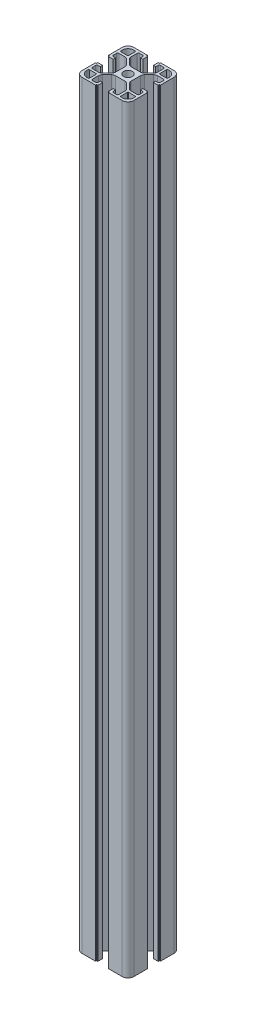
SolidWorks part; units mm, degrees
ref_plane "Front Plane" through (0, 0, 0) normal (0, 0, 1) x (1, 0, 0)
ref_plane "Top Plane" through (0, 0, 0) normal (0, 1, 0) x (1, 0, 0)
ref_plane "Right Plane" through (0, 0, 0) normal (1, 0, 0) x (0, 0, -1)
sketch "Sketch1" plane through (0, 0, 0) normal (0, 1, 0) x (1, 0, 0)
  line L0 (84.1702, 31.7204) -> (84.1702, 42.1204)
  line L1 (44.1702, 62.7204) -> (44.1702, 52.3204)
  line L2 (48.6702, 27.2204) -> (59.0702, 27.2204)
  line L3 (79.6702, 67.2204) -> (69.2702, 67.2204)
  line L4 (84.1702, 52.3204) -> (84.1702, 62.7204)
  line L6 (44.1702, 42.1204) -> (44.1702, 31.7204)
  line L7 (69.2702, 27.2204) -> (79.6702, 27.2204)
  line L10 (44.1702, 42.1204) -> (44.7702, 42.1204)
  line L11 (44.9702, 42.3204) -> (44.9702, 42.9204)
  line L12 (48.6702, 43.1204) -> (45.1702, 43.1204)
  line L13 (48.6702, 41.3204) -> (48.6702, 43.1204)
  line L14 (46.9702, 41.3204) -> (48.6702, 41.3204)
  line L15 (45.9702, 37.9704) -> (45.9702, 40.3204)
  line L16 (51.6169, 36.9704) -> (46.9702, 36.9704)
  line L17 (57.2915, 41.4024) -> (53.7382, 37.8491)
  line L18 (58.1702, 50.9171) -> (58.1702, 43.5237)
  line L19 (53.7382, 56.5917) -> (57.2915, 53.0384)
  line L20 (46.9702, 57.4704) -> (51.6169, 57.4704)
  line L21 (45.9702, 54.1204) -> (45.9702, 56.4704)
  line L22 (48.6702, 53.1204) -> (46.9702, 53.1204)
  line L23 (48.6702, 51.3204) -> (48.6702, 53.1204)
  line L24 (45.1702, 51.3204) -> (48.6702, 51.3204)
  line L25 (44.9702, 51.5204) -> (44.9702, 52.1204)
  line L26 (44.7702, 52.3204) -> (44.1702, 52.3204)
  line L28 (59.0702, 67.2204) -> (48.6702, 67.2204)
  line L29 (59.0702, 67.2204) -> (59.0702, 66.6204)
  line L30 (59.2702, 66.4204) -> (60.0702, 66.4204)
  line L31 (60.0702, 62.7204) -> (60.0702, 66.4204)
  line L32 (58.2702, 62.7204) -> (60.0702, 62.7204)
  line L33 (58.2702, 64.4204) -> (58.2702, 62.7204)
  line L34 (54.9202, 65.4204) -> (57.2702, 65.4204)
  line L35 (53.9202, 59.7737) -> (53.9202, 64.4204)
  line L36 (58.3522, 54.0991) -> (54.7989, 57.6524)
  line L37 (67.8669, 53.2204) -> (60.4735, 53.2204)
  line L38 (73.5415, 57.6524) -> (69.9882, 54.0991)
  line L39 (74.4202, 64.4204) -> (74.4202, 59.7737)
  line L40 (71.0702, 65.4204) -> (73.4202, 65.4204)
  line L41 (70.0702, 62.7204) -> (70.0702, 64.4204)
  line L42 (68.2702, 62.7204) -> (70.0702, 62.7204)
  line L43 (68.2702, 66.2204) -> (68.2702, 62.7204)
  line L44 (68.4702, 66.4204) -> (69.2702, 66.4204)
  line L45 (69.2702, 66.4204) -> (69.2702, 67.2204)
  line L48 (84.1702, 52.3204) -> (83.5702, 52.3204)
  line L49 (83.3702, 52.1204) -> (83.3702, 51.5204)
  line L50 (79.6702, 51.3204) -> (83.1702, 51.3204)
  line L51 (79.6702, 53.1204) -> (79.6702, 51.3204)
  line L52 (81.3702, 53.1204) -> (79.6702, 53.1204)
  line L53 (82.3702, 56.4704) -> (82.3702, 54.1204)
  line L54 (76.7235, 57.4704) -> (81.3702, 57.4704)
  line L55 (71.0489, 53.0384) -> (74.6022, 56.5917)
  line L56 (70.1702, 43.5237) -> (70.1702, 50.9171)
  line L57 (74.6022, 37.8491) -> (71.0489, 41.4024)
  line L58 (81.3702, 36.9704) -> (76.7235, 36.9704)
  line L59 (82.3702, 40.3204) -> (82.3702, 37.9704)
  line L60 (79.6702, 41.3204) -> (81.3702, 41.3204)
  line L61 (79.6702, 43.1204) -> (79.6702, 41.3204)
  line L62 (83.1702, 43.1204) -> (79.6702, 43.1204)
  line L63 (83.3702, 42.9204) -> (83.3702, 42.3204)
  line L64 (83.5702, 42.1204) -> (84.1702, 42.1204)
  line L67 (69.2702, 27.2204) -> (69.2702, 27.8204)
  line L68 (69.0702, 28.0204) -> (68.4702, 28.0204)
  line L69 (68.2702, 31.7204) -> (68.2702, 28.2204)
  line L70 (70.0702, 31.7204) -> (68.2702, 31.7204)
  line L71 (70.0702, 30.0204) -> (70.0702, 31.7204)
  line L72 (73.4202, 29.0204) -> (71.0702, 29.0204)
  line L73 (74.4202, 34.6671) -> (74.4202, 30.0204)
  line L74 (69.9882, 40.3417) -> (73.5415, 36.7884)
  line L75 (60.4735, 41.2204) -> (67.8669, 41.2204)
  line L76 (54.7989, 36.7884) -> (58.3522, 40.3417)
  line L77 (53.9202, 30.0204) -> (53.9202, 34.6671)
  line L78 (57.2702, 29.0204) -> (54.9202, 29.0204)
  line L79 (58.2702, 31.7204) -> (58.2702, 30.0204)
  line L80 (60.0702, 31.7204) -> (58.2702, 31.7204)
  line L81 (60.0702, 28.2204) -> (60.0702, 31.7204)
  line L82 (59.8702, 28.0204) -> (59.2702, 28.0204)
  line L83 (59.0702, 27.8204) -> (59.0702, 27.2204)
  line L84 (82.3702, 34.6704) -> (82.3702, 33.5204)
  line L85 (76.7202, 35.1704) -> (81.8702, 35.1704)
  line L86 (76.2202, 29.5204) -> (76.2202, 34.6704)
  line L87 (77.8702, 29.0204) -> (76.7202, 29.0204)
  line L88 (51.6202, 29.0204) -> (50.4702, 29.0204)
  line L89 (52.1202, 34.6704) -> (52.1202, 29.5204)
  line L90 (46.4702, 35.1704) -> (51.6202, 35.1704)
  line L91 (45.9702, 33.5204) -> (45.9702, 34.6704)
  line L92 (45.9702, 59.7704) -> (45.9702, 60.9204)
  line L93 (51.6202, 59.2704) -> (46.4702, 59.2704)
  line L94 (52.1202, 64.9204) -> (52.1202, 59.7704)
  line L95 (50.4702, 65.4204) -> (51.6202, 65.4204)
  line L96 (76.7202, 65.4204) -> (77.8702, 65.4204)
  line L97 (76.2202, 59.7704) -> (76.2202, 64.9204)
  line L98 (81.8702, 59.2704) -> (76.7202, 59.2704)
  line L99 (82.3702, 60.9204) -> (82.3702, 59.7704)
  arc A0 (60.7702, 47.2204) -> (67.5702, 47.2204) centre (64.1702, 47.2204) ccw
  arc A1 (44.1702, 31.7204) -> (48.6702, 27.2204) centre (48.6702, 31.7204) ccw
  arc A2 (44.7702, 42.1204) -> (44.9702, 42.3204) centre (44.7702, 42.3204) ccw
  arc A3 (45.1702, 43.1204) -> (44.9702, 42.9204) centre (45.1702, 42.9204) ccw
  arc A4 (46.9702, 41.3204) -> (45.9702, 40.3204) centre (46.9702, 40.3204) ccw
  arc A5 (45.9702, 37.9704) -> (46.9702, 36.9704) centre (46.9702, 37.9704) ccw
  arc A6 (51.6169, 36.9704) -> (53.7382, 37.8491) centre (51.6169, 39.9704) ccw
  arc A7 (57.2915, 41.4024) -> (58.1702, 43.5237) centre (55.1702, 43.5237) ccw
  arc A8 (58.1702, 50.9171) -> (57.2915, 53.0384) centre (55.1702, 50.9171) ccw
  arc A9 (53.7382, 56.5917) -> (51.6169, 57.4704) centre (51.6169, 54.4704) ccw
  arc A10 (46.9702, 57.4704) -> (45.9702, 56.4704) centre (46.9702, 56.4704) ccw
  arc A11 (45.9702, 54.1204) -> (46.9702, 53.1204) centre (46.9702, 54.1204) ccw
  arc A12 (44.9702, 51.5204) -> (45.1702, 51.3204) centre (45.1702, 51.5204) ccw
  arc A13 (44.9702, 52.1204) -> (44.7702, 52.3204) centre (44.7702, 52.1204) ccw
  arc A14 (48.6702, 67.2204) -> (44.1702, 62.7204) centre (48.6702, 62.7204) ccw
  arc A15 (59.0702, 66.6204) -> (59.2702, 66.4204) centre (59.2702, 66.6204) ccw
  arc A16 (58.2702, 64.4204) -> (57.2702, 65.4204) centre (57.2702, 64.4204) ccw
  arc A17 (54.9202, 65.4204) -> (53.9202, 64.4204) centre (54.9202, 64.4204) ccw
  arc A18 (53.9202, 59.7737) -> (54.7989, 57.6524) centre (56.9202, 59.7737) ccw
  arc A19 (58.3522, 54.0991) -> (60.4735, 53.2204) centre (60.4735, 56.2204) ccw
  arc A20 (67.8669, 53.2204) -> (69.9882, 54.0991) centre (67.8669, 56.2204) ccw
  arc A21 (73.5415, 57.6524) -> (74.4202, 59.7737) centre (71.4202, 59.7737) ccw
  arc A22 (74.4202, 64.4204) -> (73.4202, 65.4204) centre (73.4202, 64.4204) ccw
  arc A23 (71.0702, 65.4204) -> (70.0702, 64.4204) centre (71.0702, 64.4204) ccw
  arc A24 (68.4702, 66.4204) -> (68.2702, 66.2204) centre (68.4702, 66.2204) ccw
  arc A25 (84.1702, 62.7204) -> (79.6702, 67.2204) centre (79.6702, 62.7204) ccw
  arc A26 (83.5702, 52.3204) -> (83.3702, 52.1204) centre (83.5702, 52.1204) ccw
  arc A27 (83.1702, 51.3204) -> (83.3702, 51.5204) centre (83.1702, 51.5204) ccw
  arc A28 (81.3702, 53.1204) -> (82.3702, 54.1204) centre (81.3702, 54.1204) ccw
  arc A29 (82.3702, 56.4704) -> (81.3702, 57.4704) centre (81.3702, 56.4704) ccw
  arc A30 (76.7235, 57.4704) -> (74.6022, 56.5917) centre (76.7235, 54.4704) ccw
  arc A31 (71.0489, 53.0384) -> (70.1702, 50.9171) centre (73.1702, 50.9171) ccw
  arc A32 (70.1702, 43.5237) -> (71.0489, 41.4024) centre (73.1702, 43.5237) ccw
  arc A33 (74.6022, 37.8491) -> (76.7235, 36.9704) centre (76.7235, 39.9704) ccw
  arc A34 (81.3702, 36.9704) -> (82.3702, 37.9704) centre (81.3702, 37.9704) ccw
  arc A35 (82.3702, 40.3204) -> (81.3702, 41.3204) centre (81.3702, 40.3204) ccw
  arc A36 (83.3702, 42.9204) -> (83.1702, 43.1204) centre (83.1702, 42.9204) ccw
  arc A37 (83.3702, 42.3204) -> (83.5702, 42.1204) centre (83.5702, 42.3204) ccw
  arc A38 (79.6702, 27.2204) -> (84.1702, 31.7204) centre (79.6702, 31.7204) ccw
  arc A39 (69.2702, 27.8204) -> (69.0702, 28.0204) centre (69.0702, 27.8204) ccw
  arc A40 (68.2702, 28.2204) -> (68.4702, 28.0204) centre (68.4702, 28.2204) ccw
  arc A41 (70.0702, 30.0204) -> (71.0702, 29.0204) centre (71.0702, 30.0204) ccw
  arc A42 (73.4202, 29.0204) -> (74.4202, 30.0204) centre (73.4202, 30.0204) ccw
  arc A43 (74.4202, 34.6671) -> (73.5415, 36.7884) centre (71.4202, 34.6671) ccw
  arc A44 (69.9882, 40.3417) -> (67.8669, 41.2204) centre (67.8669, 38.2204) ccw
  arc A45 (60.4735, 41.2204) -> (58.3522, 40.3417) centre (60.4735, 38.2204) ccw
  arc A46 (54.7989, 36.7884) -> (53.9202, 34.6671) centre (56.9202, 34.6671) ccw
  arc A47 (53.9202, 30.0204) -> (54.9202, 29.0204) centre (54.9202, 30.0204) ccw
  arc A48 (57.2702, 29.0204) -> (58.2702, 30.0204) centre (57.2702, 30.0204) ccw
  arc A49 (59.8702, 28.0204) -> (60.0702, 28.2204) centre (59.8702, 28.2204) ccw
  arc A50 (59.2702, 28.0204) -> (59.0702, 27.8204) centre (59.2702, 27.8204) ccw
  arc A51 (82.3702, 34.6704) -> (81.8702, 35.1704) centre (81.8702, 34.6704) ccw
  arc A52 (76.7202, 35.1704) -> (76.2202, 34.6704) centre (76.7202, 34.6704) ccw
  arc A53 (76.2202, 29.5204) -> (76.7202, 29.0204) centre (76.7202, 29.5204) ccw
  arc A54 (77.8702, 29.0204) -> (82.3702, 33.5204) centre (77.8702, 33.5204) ccw
  arc A55 (51.6202, 29.0204) -> (52.1202, 29.5204) centre (51.6202, 29.5204) ccw
  arc A56 (52.1202, 34.6704) -> (51.6202, 35.1704) centre (51.6202, 34.6704) ccw
  arc A57 (46.4702, 35.1704) -> (45.9702, 34.6704) centre (46.4702, 34.6704) ccw
  arc A58 (45.9702, 33.5204) -> (50.4702, 29.0204) centre (50.4702, 33.5204) ccw
  arc A59 (45.9702, 59.7704) -> (46.4702, 59.2704) centre (46.4702, 59.7704) ccw
  arc A60 (51.6202, 59.2704) -> (52.1202, 59.7704) centre (51.6202, 59.7704) ccw
  arc A61 (52.1202, 64.9204) -> (51.6202, 65.4204) centre (51.6202, 64.9204) ccw
  arc A62 (50.4702, 65.4204) -> (45.9702, 60.9204) centre (50.4702, 60.9204) ccw
  arc A63 (76.7202, 65.4204) -> (76.2202, 64.9204) centre (76.7202, 64.9204) ccw
  arc A64 (76.2202, 59.7704) -> (76.7202, 59.2704) centre (76.7202, 59.7704) ccw
  arc A65 (81.8702, 59.2704) -> (82.3702, 59.7704) centre (81.8702, 59.7704) ccw
  arc A66 (82.3702, 60.9204) -> (77.8702, 65.4204) centre (77.8702, 60.9204) ccw
  arc A67 (67.5702, 47.2204) -> (60.7702, 47.2204) centre (64.1702, 47.2204) ccw
extrude "Boss-Extrude1" add sketch "Sketch1" along normal blind 586
